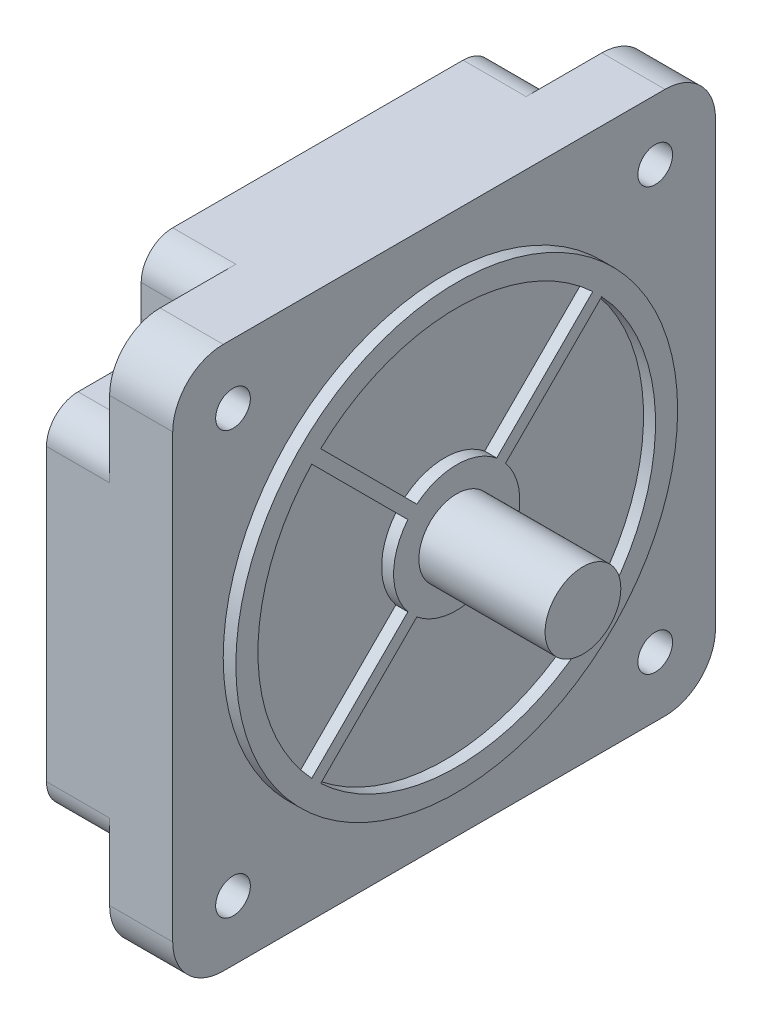
SolidWorks part; units mm, degrees
ref_plane "Front Plane" through (0, 0, 0) normal (0, 0, 1) x (1, 0, 0)
ref_plane "Top Plane" through (0, 0, 0) normal (0, 1, 0) x (1, 0, 0)
ref_plane "Right Plane" through (0, 0, 0) normal (1, 0, 0) x (0, 0, -1)
sketch "Sketch1" plane through (0, 0, 0) normal (1, 0, 0) x (0, 0, -1)
  line L1 (8, 0) -> (78, 0)
  line L2 (0, 8) -> (0, 78)
  line L3 (8, 86) -> (78, 86)
  line L4 (86, 8) -> (86, 78)
  arc A0 (8, 0) -> (0, 8) centre (8, 8) cw
  arc A1 (78, 0) -> (86, 8) centre (78, 8) ccw
  arc A2 (78, 86) -> (86, 78) centre (78, 78) cw
  arc A3 (0, 78) -> (8, 86) centre (8, 78) cw
  point P7 (0, 0)
  point P10 (86, 0)
  point P13 (86, 86)
  dimension "D3" = 8
  dimension "D1" = 86
  dimension "D2" = 86
extrude "Boss-Extrude1" add sketch "Sketch1" along normal blind 20
sketch "Sketch2" plane through (0, 0, 0) normal (-1, 0, 0) x (0, 0, 1)
  line L0 (-15, 86) -> (-15, 76)
  line L1 (-10, 71) -> (0, 71)
  line L2 (-78, 86) -> (-8, 86) construction
  line L3 (-43, 86) -> (-43, 0) construction
  line L4 (-8, 0) -> (-78, 0) construction
  line L5 (-15, 86) -> (-8, 86)
  line L6 (0, 78) -> (0, 71)
  line L7 (0, 78) -> (0, 8) construction
  line L8 (0, 43) -> (-86, 43) construction
  line L9 (-86, 8) -> (-86, 78) construction
  line L10 (-76, 71) -> (-86, 71)
  line L12 (-86, 78) -> (-86, 71)
  line L13 (-71, 86) -> (-78, 86)
  line L14 (-71, 86) -> (-71, 76)
  line L16 (-15, 86) -> (-15, 71)
  line L17 (-15, 86) -> (-8, 86)
  line L18 (0, 78) -> (0, 71)
  line L19 (-15, 71) -> (0, 71)
  line L20 (-86, 78) -> (-86, 71)
  line L21 (-71, 86) -> (-78, 86)
  line L22 (-71, 71) -> (-86, 71)
  line L23 (-71, 86) -> (-71, 71)
  line L24 (-10, 15) -> (0, 15)
  line L25 (0, 8) -> (0, 15)
  line L26 (-15, 0) -> (-8, 0)
  line L27 (-15, 0) -> (-15, 10)
  line L28 (0, 8) -> (0, 15)
  line L29 (-15, 0) -> (-8, 0)
  line L30 (-15, 15) -> (0, 15)
  line L31 (-15, 0) -> (-15, 15)
  line L32 (-71, 0) -> (-71, 10)
  line L33 (-76, 15) -> (-86, 15)
  line L34 (-71, 0) -> (-78, 0)
  line L35 (-86, 8) -> (-86, 15)
  line L36 (-71, 0) -> (-71, 15)
  line L37 (-71, 0) -> (-78, 0)
  line L38 (-86, 8) -> (-86, 15)
  line L39 (-71, 15) -> (-86, 15)
  arc A0 (-8, 86) -> (0, 78) centre (-8, 78) cw
  arc A1 (-78, 86) -> (-86, 78) centre (-78, 78) ccw
  arc A2 (-8, 86) -> (0, 78) centre (-8, 78) cw
  arc A3 (-78, 86) -> (-86, 78) centre (-78, 78) ccw
  arc A4 (-8, 0) -> (0, 8) centre (-8, 8) ccw
  arc A5 (-8, 0) -> (0, 8) centre (-8, 8) ccw
  arc A6 (-78, 0) -> (-86, 8) centre (-78, 8) cw
  arc A7 (-78, 0) -> (-86, 8) centre (-78, 8) cw
  arc A8 (-71, 10) -> (-76, 15) centre (-76, 10) ccw
  arc A9 (-10, 15) -> (-15, 10) centre (-10, 10) ccw
  arc A10 (-15, 76) -> (-10, 71) centre (-10, 76) ccw
  arc A11 (-76, 71) -> (-71, 76) centre (-76, 76) ccw
  point P64 (0, 71)
  point P70 (-15, 86)
  arc M14 (-8, 0) -> (0, 8) centre (-8, 8) ccw
  line M15 (0, 8) -> (0, 78)
  arc M16 (0, 78) -> (-8, 86) centre (-8, 78) ccw
  line M17 (-8, 86) -> (-78, 86)
  arc M18 (-78, 86) -> (-86, 78) centre (-78, 78) ccw
  line M19 (-86, 78) -> (-86, 8)
  arc M20 (-86, 8) -> (-78, 0) centre (-78, 8) ccw
  line M21 (-78, 0) -> (-8, 0)
  dimension "D2" = 15
  dimension "D3" = 8
  dimension "D4" = 5
  dimension "D1" = 15
extrude "Cut-Extrude1" cut sketch "Sketch2" against normal blind 10 contours L10 A11 L14 M17 M18 M19 | L0 A10 L1 M15 M16 M17 | L24 A9 L27 M21 M14 M15 | L32 A8 L33 M19 M20 M21
fillet "Fillet1" radius 5 8 edges at (5, 86, -71) (5, 86, -15) (5, 71, 0) (5, 15, 0) (5, 0, -15) (5, 0, -71) (5, 15, -86) (5, 71, -86)
sketch "Sketch3" plane through (20, 0, 0) normal (1, 0, 0) x (0, 0, -1)
  line L0 (2.3431, 83.6569) -> (83.6569, 2.3431) construction
  line L1 (9.55, 76.45) -> (76.45, 76.45) construction
  line L2 (9.55, 76.45) -> (9.55, 9.55) construction
  line L3 (9.55, 9.55) -> (76.45, 9.55) construction
  line L4 (76.45, 76.45) -> (76.45, 9.55) construction
  line L5 (2.3431, 2.3431) -> (83.6569, 83.6569) construction
  arc A0 (8, 86) -> (0, 78) centre (8, 78) ccw construction
  arc A1 (78, 0) -> (86, 8) centre (78, 8) ccw construction
  arc A2 (0, 8) -> (8, 0) centre (8, 8) ccw construction
  arc A3 (86, 78) -> (78, 86) centre (78, 78) ccw construction
  circle A4 centre (9.55, 76.45) radius 2.75
  circle A5 centre (76.45, 76.45) radius 2.75
  circle A6 centre (76.45, 9.55) radius 2.75
  circle A7 centre (9.55, 9.55) radius 2.75
  dimension "D2" = 5.5
  dimension "D1" = 66.9
extrude "Cut-Extrude2" cut sketch "Sketch3" against normal blind 10
sketch "Sketch4" plane through (20, 0, 0) normal (1, 0, 0) x (0, 0, -1)
  line L0 (2.3431, 83.6569) -> (83.6569, 2.3431) construction
  arc A0 (8, 86) -> (0, 78) centre (8, 78) ccw construction
  arc A1 (78, 0) -> (86, 8) centre (78, 8) ccw construction
  circle A2 centre (43, 43) radius 6
  dimension "D1" = 12
extrude "Boss-Extrude3" add sketch "Sketch4" along normal blind 22
sketch "Sketch5" plane through (20, 0, 0) normal (1, 0, 0) x (0, 0, -1)
  circle A0 centre (43, 43) radius 35
  circle A1 centre (43, 43) radius 10
  circle A2 centre (43, 43) radius 6
  circle A3 centre (43, 43) radius 6 construction
  circle A4 centre (43, 43) radius 31.5
  dimension "D1" = 70
  dimension "D2" = 20
  dimension "D3" = 63
extrude "Boss-Extrude4" add sketch "Sketch5" along normal blind 2 contours A0 | A4 | A1 | A2
sketch "Sketch6" plane through (20, 0, 0) normal (1, 0, 0) x (0, 0, -1)
  circle A0 centre (43, 43) radius 31.5
  circle A1 centre (43, 43) radius 10
  circle A2 centre (43, 43) radius 10 construction
  circle A3 centre (43, 43) radius 31.5 construction
extrude "Boss-Extrude5" add sketch "Sketch6" along normal blind 0.1
sketch "Sketch7" plane through (20, 0, 0) normal (1, 0, 0) x (0, 0, -1)
  line L0 (2.3431, 83.6569) -> (83.6569, 2.3431) construction
  line L1 (2.3431, 2.3431) -> (83.6569, 83.6569) construction
  line L2 (37.3431, 50.0711) -> (35.9289, 48.6569)
  line L3 (35.9289, 48.6569) -> (19.6655, 64.9203)
  line L4 (19.6655, 64.9203) -> (21.0797, 66.3345)
  line L5 (21.0797, 66.3345) -> (37.3431, 50.0711)
  line L6 (0, 43) -> (86, 43) construction
  line L7 (0, 78) -> (0, 8) construction
  line L8 (86, 8) -> (86, 78) construction
  line L9 (21.0797, 19.6655) -> (37.3431, 35.9289)
  line L10 (19.6655, 21.0797) -> (21.0797, 19.6655)
  line L11 (35.9289, 37.3431) -> (19.6655, 21.0797)
  line L12 (37.3431, 35.9289) -> (35.9289, 37.3431)
  line L13 (66.3345, 21.0797) -> (50.0711, 37.3431)
  line L14 (64.9203, 19.6655) -> (66.3345, 21.0797)
  line L15 (48.6569, 35.9289) -> (64.9203, 19.6655)
  line L16 (50.0711, 37.3431) -> (48.6569, 35.9289)
  line L17 (43, 86) -> (43, 0) construction
  line L18 (78, 86) -> (8, 86) construction
  line L19 (8, 0) -> (78, 0) construction
  line L20 (64.9203, 66.3345) -> (48.6569, 50.0711)
  line L21 (66.3345, 64.9203) -> (64.9203, 66.3345)
  line L22 (50.0711, 48.6569) -> (66.3345, 64.9203)
  line L23 (48.6569, 50.0711) -> (50.0711, 48.6569)
  arc A0 (8, 86) -> (0, 78) centre (8, 78) ccw construction
  arc A1 (78, 0) -> (86, 8) centre (78, 8) ccw construction
  arc A2 (0, 8) -> (8, 0) centre (8, 8) ccw construction
  arc A3 (86, 78) -> (78, 86) centre (78, 78) ccw construction
  point P16 (36.636, 49.364)
  point P23 (43, 43)
  dimension "D1" = 23
  dimension "D2" = 2
  dimension "D3" = 9
extrude "Boss-Extrude6" add sketch "Sketch7" along normal blind 2
